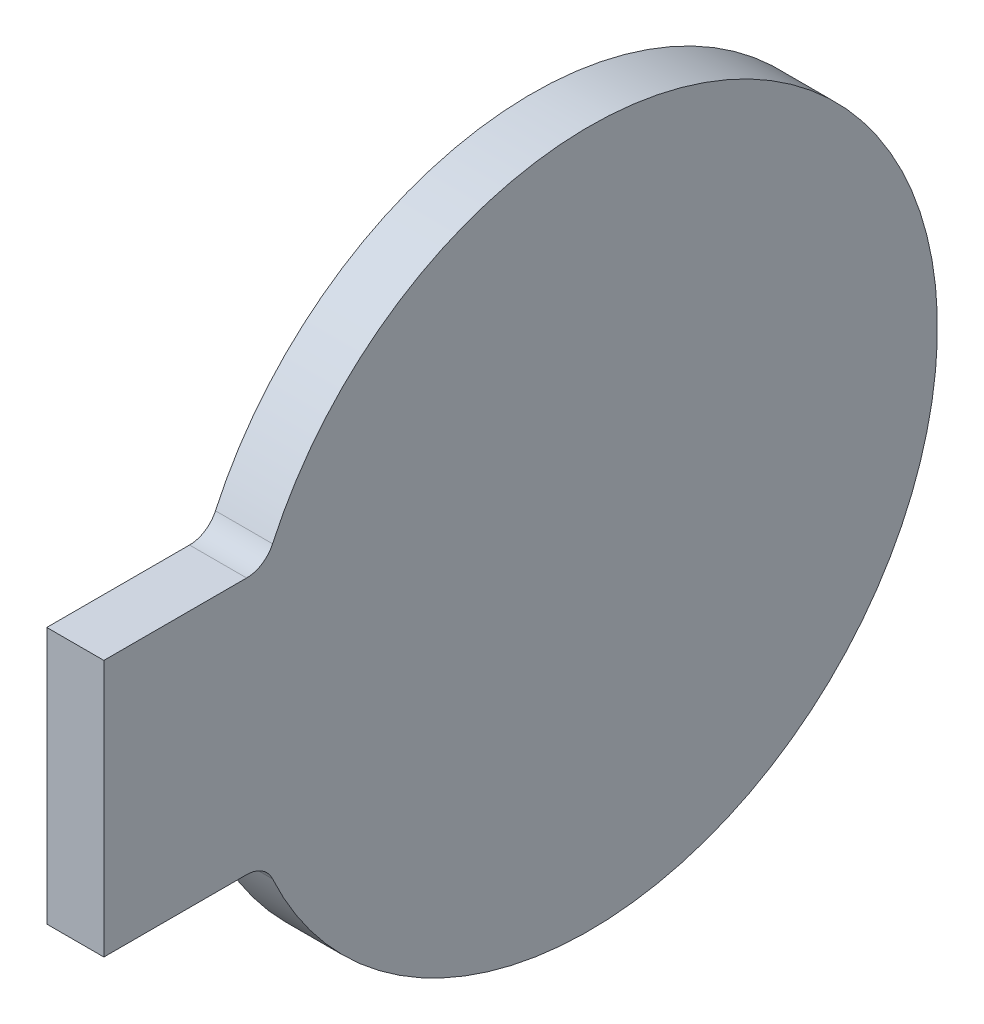
SolidWorks part; units mm, degrees
ref_plane "前视基准面" through (0, 0, 0) normal (0, 0, 1) x (1, 0, 0)
ref_plane "上视基准面" through (0, 0, 0) normal (0, 1, 0) x (1, 0, 0)
ref_plane "右视基准面" through (0, 0, 0) normal (1, 0, 0) x (0, 0, -1)
sketch "草图1" plane through (0, 0, 0) normal (0, 1, 0) x (1, 0, 0)
  line L1 (0, 0) -> (-2, 0)
  line L2 (0, 0) -> (0, -12.2)
  line L3 (0, -12.2) -> (-2, -12.2)
  line L4 (-2, 0) -> (-2, -12.2)
  dimension "D1" = 2
  dimension "D2" = 12.2
revolve "旋转1" add sketch "草图1" angle 360 about L1
sketch "草图2" plane through (0, 0, 0) normal (0, 0, 1) x (1, 0, 0)
  line L0 (-2, 4.5) -> (-2, -4.5)
  line L1 (-2, 12.2) -> (-2, -12.2) construction
  line L2 (-2, -4.5) -> (0, -4.5)
  line L3 (0, -12.2) -> (0, 12.2) construction
  line L4 (0, -4.5) -> (0, 4.5)
  line L5 (-1002, 0) -> (48998, 0) construction
  line L6 (-2, 4.5) -> (0, 4.5)
  point P12 (0, 0)
  point P13 (-2, 0)
  dimension "D1" = 4.5
extrude "凸台-拉伸1" add sketch "草图2" along normal blind 17
fillet "圆角3" radius 1 2 edges at (-1, -4.5, 11.3398) (-1, 4.5, 11.3398)
